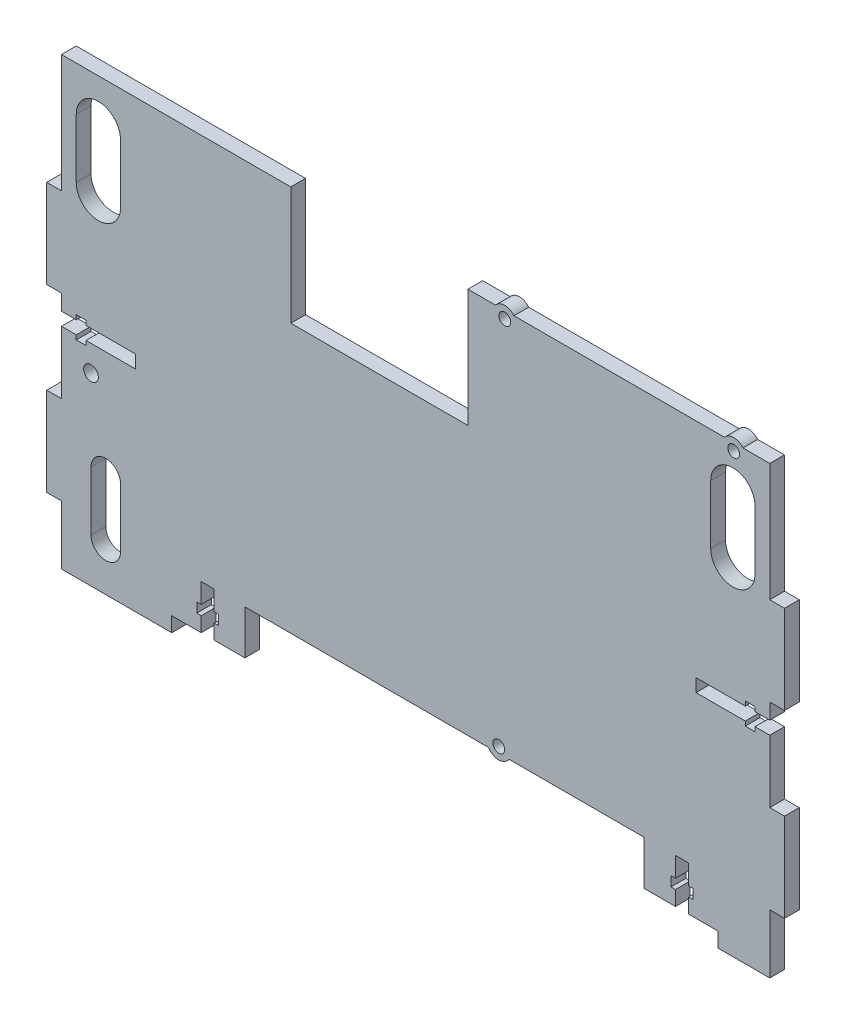
SolidWorks part; units mm, degrees
ref_plane "Front Plane" through (0, 0, 0) normal (0, 0, 1) x (1, 0, 0)
ref_plane "Top Plane" through (0, 0, 0) normal (0, 1, 0) x (1, 0, 0)
ref_plane "Right Plane" through (0, 0, 0) normal (1, 0, 0) x (0, 0, -1)
sketch "Sketch1" plane through (0, 0, 0) normal (0, 0, 1) x (1, 0, 0)
  line L1 (-120, 75.5) -> (120, 75.5)
  line L2 (-120, 75.5) -> (-120, -75.5)
  line L3 (-120, -75.5) -> (120, -75.5)
  line L4 (120, 75.5) -> (120, -75.5)
  dimension "D1" = 240
  dimension "D2" = 120
  dimension "D3" = 151
  dimension "D4" = 75.5
extrude "Boss-Extrude1" add sketch "Sketch1" along normal blind 5
sketch "Sketch2" plane through (0, 0, 0) normal (0, 0, -1) x (-1, 0, 0)
  line L1 (42.3015, 35.5) -> (42.3015, 75.5)
  line L3 (-17.6985, 75.5) -> (-17.6985, 35.5)
  line L4 (-120, 75.5) -> (120, 75.5) construction
  line L5 (42.3015, 35.5) -> (-17.6985, 35.5)
  line L6 (42.3015, 75.5) -> (-17.6985, 75.5)
  line L7 (-120, -75.5) -> (-120, 75.5) construction
  dimension "D1" = 60
  dimension "D2" = 102.3015
extrude "Cut-Extrude1" cut sketch "Sketch2" against normal blind 5
sketch "Sketch4" plane through (0, 0, 0) normal (0, 0, -1) x (-1, 0, 0)
  circle A0 centre (-107.8, 73) radius 2
  circle A1 centre (-30.2, 73) radius 2
  dimension "D1" = 4
  dimension "D2" = 4
extrude "Cut-Extrude3" cut sketch "Sketch4" against normal blind 5
sketch "Sketch5" plane through (0, 0, 0) normal (0, 0, -1) x (-1, 0, 0)
  circle A0 centre (-30.2, 73) radius 2
  circle A1 centre (-107.8, 73) radius 2
  circle A2 centre (-30.2, 73) radius 4
  circle A3 centre (-107.8, 73) radius 4
  dimension "D1" = 8
  dimension "D2" = 8
extrude "Boss-Extrude2" add sketch "Sketch5" against normal blind 5
sketch "Sketch6" plane through (0, 0, 0) normal (0, 0, -1) x (-1, 0, 0)
  circle A0 centre (117.5, 7.7) radius 2
  circle A1 centre (117.5, 63.3) radius 2
  dimension "D1" = 4
  dimension "D2" = 4
extrude "Cut-Extrude4" [suppressed] cut sketch "Sketch6" against normal blind 5
sketch "Sketch7" [suppressed] plane through (0, 0, 0) normal (0, 0, -1) x (-1, 0, 0)
  circle A0 centre (117.5, 7.7) radius 2
  circle A1 centre (117.5, 63.3) radius 1.9875
  circle A2 centre (117.5, 7.7) radius 4
  circle A3 centre (117.5, 63.3) radius 4
  dimension "D1" = 8
  dimension "D2" = 8
extrude "Boss-Extrude3" [suppressed] add sketch "Sketch7" against normal blind 5
sketch "Sketch8" plane through (0, 0, 0) normal (0, 0, -1) x (-1, 0, 0)
  line L0 (105, -60.5) -> (105, -40.5) construction
  line L1 (100, -60.5) -> (100, -40.5)
  line L2 (110, -60.5) -> (110, -40.5)
  line L3 (120, -75.5) -> (-120, -75.5) construction
  line L4 (120, 75.5) -> (120, -75.5) construction
  line L5 (0, 0) -> (0, -55.5387) construction
  arc A0 (100, -60.5) -> (110, -60.5) centre (105, -60.5) ccw
  arc A1 (110, -40.5) -> (100, -40.5) centre (105, -40.5) ccw
  point P2 (105, -50.5)
  point P17 (-92, -45.5)
  dimension "D1" = 20
  dimension "D2" = 15
  dimension "D3" = 10
  dimension "D4" = 10
extrude "Cut-Extrude5" cut sketch "Sketch8" against normal blind 5
sketch "Sketch9" plane through (0, 0, 0) normal (0, 0, -1) x (-1, 0, 0)
  circle A0 centre (117.5, 44.8) radius 2
  circle A1 centre (117.5, -10.8) radius 2
  dimension "D1" = 4
  dimension "D2" = 4
extrude "Cut-Extrude6" [suppressed] cut sketch "Sketch9" against normal blind 5
sketch "Sketch10" [suppressed] plane through (0, 0, 0) normal (0, 0, -1) x (-1, 0, 0)
  circle A0 centre (117.5, -10.8) radius 2
  circle A1 centre (117.5, -10.8) radius 4
  circle A2 centre (117.5, 44.8) radius 2
  circle A3 centre (117.5, 44.8) radius 4
  dimension "D1" = 8
  dimension "D2" = 8
extrude "Boss-Extrude4" [suppressed] add sketch "Sketch10" against normal blind 5
sketch "Sketch12" plane through (0, 0, 0) normal (0, 0, -1) x (-1, 0, 0)
  circle A0 centre (-28.1604, -53.4404) radius 2
  dimension "D1" = 4
extrude "Cut-Extrude7" cut sketch "Sketch12" against normal blind 5
sketch "Sketch13" plane through (0, 0, 0) normal (0, 0, -1) x (-1, 0, 0)
  circle A1 centre (110, -13) radius 2.5
extrude "Cut-Extrude8" cut sketch "Sketch13" against normal blind 10
sketch "Sketch14" plane through (0, 0, 0) normal (0, 0, -1) x (-1, 0, 0)
  line L0 (-104.6775, 75.5) -> (-33.3225, 75.5) construction
  line L1 (-120, -75.5) -> (-120, 75.5) construction
  line L2 (120, -75.5) -> (-120, -75.5) construction
  line L3 (120, 75.5) -> (120, -75.5) construction
  line L4 (42.3015, 75.5) -> (120, 75.5) construction
  circle A0 centre (-105, -60.5) radius 2.5
  circle A1 centre (105, -60.5) radius 2.5
  circle A2 centre (-105, 60.5) radius 2.5
  circle A3 centre (105, 60.5) radius 2.5
  dimension "D1" = 5
  dimension "D2" = 5
  dimension "D3" = 5
  dimension "D4" = 5
  dimension "D5" = 15
  dimension "D6" = 15
  dimension "D7" = 15
  dimension "D8" = 15
  dimension "D9" = 15
  dimension "D10" = 15
  dimension "D11" = 15
  dimension "D12" = 15
extrude "Cut-Extrude9" [suppressed] cut sketch "Sketch14" against normal blind 10
sketch "Sketch15" plane through (0, 0, 0) normal (0, 0, -1) x (-1, 0, 0)
  line L0 (-70, 0) -> (-50, 0) construction
  line L1 (-70, 7.5) -> (-50, 7.5)
  line L2 (-70, -7.5) -> (-50, -7.5)
  line L3 (50, 0) -> (70, 0) construction
  line L4 (50, 7.5) -> (70, 7.5)
  line L5 (50, -7.5) -> (70, -7.5)
  line L6 (-102.5, 55.5) -> (-102.5, 35.5) construction
  line L7 (-95, 55.5) -> (-95, 35.5)
  line L8 (-110, 55.5) -> (-110, 35.5)
  line L9 (-104.6775, 75.5) -> (-33.3225, 75.5) construction
  line L10 (-120, -75.5) -> (-120, 75.5) construction
  line L11 (0, 0) -> (0, 86.6929) construction
  line L12 (102.5, 55.5) -> (102.5, 35.5) construction
  line L13 (95, 55.5) -> (95, 35.5)
  line L14 (110, 55.5) -> (110, 35.5)
  arc A0 (-70, 7.5) -> (-70, -7.5) centre (-70, 0) ccw
  arc A1 (-50, -7.5) -> (-50, 7.5) centre (-50, 0) ccw
  arc A2 (50, 7.5) -> (50, -7.5) centre (50, 0) ccw
  arc A3 (70, -7.5) -> (70, 7.5) centre (70, 0) ccw
  arc A4 (-95, 55.5) -> (-110, 55.5) centre (-102.5, 55.5) ccw
  arc A5 (-110, 35.5) -> (-95, 35.5) centre (-102.5, 35.5) ccw
  arc A6 (95, 55.5) -> (110, 55.5) centre (102.5, 55.5) cw
  arc A7 (110, 35.5) -> (95, 35.5) centre (102.5, 35.5) cw
  point P2 (-60, 0)
  point P7 (60, 0)
  point P14 (-60, 7.5)
  point P15 (60, -7.5)
  point P16 (-102.5, 45.5)
  point P32 (102.5, 45.5)
  dimension "D1" = 20
  dimension "D2" = 20
  dimension "D3" = 50
  dimension "D4" = 50
  dimension "D5" = 15
  dimension "D6" = 15
  dimension "D7" = 15
  dimension "D8" = 20
  dimension "D9" = 20
  dimension "D10" = 10
extrude "Cut-Extrude10" [suppressed] cut sketch "Sketch15" against normal blind 10
sketch "Sketch16" plane through (0, 0, 0) normal (0, 0, -1) x (-1, 0, 0)
  line L0 (-120, -75.5) -> (-120, 75.5) construction
  line L9 (-120, 35.5) -> (-125, 35.5)
  line L10 (-120, 35.5) -> (-120, 5.5)
  line L11 (-120, 5.5) -> (-125, 5.5)
  line L12 (-125, 35.5) -> (-125, 5.5)
  line L13 (-120, -55.5) -> (-125, -55.5)
  line L14 (-120, -55.5) -> (-120, -25.5)
  line L15 (-120, -25.5) -> (-125, -25.5)
  line L16 (-125, -55.5) -> (-125, -25.5)
  line L18 (-120, 75.5) -> (-110.9225, 75.5) construction
  line L19 (120, -75.5) -> (-120, -75.5) construction
  line L20 (0, 0) -> (0, -42.8978) construction
  line L21 (125, -55.5) -> (125, -25.5)
  line L22 (120, -25.5) -> (125, -25.5)
  line L23 (120, -55.5) -> (120, -25.5)
  line L24 (120, -55.5) -> (125, -55.5)
  line L25 (125, 35.5) -> (125, 5.5)
  line L26 (120, 5.5) -> (125, 5.5)
  line L27 (120, 35.5) -> (120, 5.5)
  line L28 (120, 35.5) -> (125, 35.5)
  dimension "D1" = 40
  dimension "D2" = 30
  dimension "D3" = 5
  dimension "D4" = 20
  dimension "D5" = 30
  dimension "D6" = 5
extrude "Boss-Extrude5" add sketch "Sketch16" against normal blind 5
sketch "Sketch17" plane through (0, 0, 0) normal (0, 0, -1) x (-1, 0, 0)
  line L0 (0, 0) -> (0, 39.4066) construction
  line L1 (-120, 0.155) -> (-115, 0.155)
  line L2 (-115, 0.155) -> (-115, 1.655)
  line L3 (-115, 1.655) -> (-111.7, 1.655)
  line L4 (-111.7, 1.655) -> (-111.7, 0.155)
  line L5 (-111.7, 0.155) -> (-95, 0.155)
  line L6 (-95, 0.155) -> (-95, -4.245)
  line L7 (-95, -4.245) -> (-111.7, -4.245)
  line L8 (-111.7, -4.245) -> (-111.7, -5.745)
  line L9 (-111.7, -5.745) -> (-115, -5.745)
  line L10 (-115, -5.745) -> (-115, -4.245)
  line L11 (-115, -4.245) -> (-120, -4.245)
  line L12 (-120, -4.245) -> (-120, 0.155)
  line L15 (-120, 35.5) -> (-120, 75.5) construction
  line L16 (120, -4.245) -> (120, 0.155)
  line L17 (115, -4.245) -> (120, -4.245)
  line L18 (115, -5.745) -> (115, -4.245)
  line L19 (111.7, -5.745) -> (115, -5.745)
  line L20 (111.7, -4.245) -> (111.7, -5.745)
  line L21 (95, -4.245) -> (111.7, -4.245)
  line L22 (95, 0.155) -> (95, -4.245)
  line L23 (111.7, 0.155) -> (95, 0.155)
  line L24 (111.7, 1.655) -> (111.7, 0.155)
  line L25 (115, 1.655) -> (111.7, 1.655)
  line L26 (115, 0.155) -> (115, 1.655)
  line L27 (120, 0.155) -> (115, 0.155)
  dimension "D1" = 4.4
  dimension "D2" = 1.5
  dimension "D3" = 3.3
  dimension "D4" = 5
  dimension "D5" = 25
extrude "Cut-Extrude11" cut sketch "Sketch17" against normal blind 5
sketch "Sketch18" plane through (0, 0, 0) normal (0, 0, -1) x (-1, 0, 0)
  line L1 (-77.45, -55.5) -> (-77.45, -75.5)
  line L3 (57.85, -75.5) -> (57.85, -55.5)
  line L5 (-77.45, -55.5) -> (57.85, -55.5)
  line L7 (-77.45, -75.5) -> (57.85, -75.5)
  line L8 (120, -55.5) -> (120, -75.5) construction
  line L9 (-120, -75.5) -> (-120, -55.5) construction
  line L10 (120, -75.5) -> (-120, -75.5) construction
  point P8 (120, -65.5)
  dimension "D1" = 62.15
  dimension "D2" = 42.55
  dimension "D3" = 20
extrude "Cut-Extrude13" cut sketch "Sketch18" against normal blind 10
sketch "Sketch19" plane through (0, 0, 0) normal (0, 0, -1) x (-1, 0, 0)
  circle A0 centre (-28.1604, -53.4404) radius 2
  circle A1 centre (-28.1604, -53.4404) radius 4
  dimension "D1" = 8
extrude "Boss-Extrude6" add sketch "Sketch19" against normal blind 5
sketch "Sketch20" plane through (0, 0, 0) normal (0, 0, -1) x (-1, 0, 0)
  line L4 (57.85, -70.5) -> (57.85, -75.5)
  line L5 (57.85, -75.5) -> (82.65, -75.5)
  line L6 (82.65, -70.5) -> (82.65, -75.5)
  line L7 (57.85, -70.5) -> (82.65, -70.5)
  line L9 (57.85, -75.5) -> (57.85, -55.5) construction
  line L10 (120, -55.5) -> (120, -75.5) construction
  dimension "D1" = 37.35
extrude "Cut-Extrude14" cut sketch "Sketch20" against normal blind 5
sketch "Sketch21" plane through (0, 0, 0) normal (0, 0, -1) x (-1, 0, 0)
  line L0 (-120, -75.5) -> (-120, -55.5) construction
  line L1 (-77.45, -55.5) -> (-77.45, -75.5) construction
  line L8 (-102.45, -75.5) -> (-77.45, -75.5)
  line L9 (-102.45, -70.5) -> (-102.45, -75.5)
  line L10 (-77.45, -70.5) -> (-102.45, -70.5)
  line L11 (-77.45, -75.5) -> (-77.45, -70.5)
  dimension "D1" = 17.55
extrude "Cut-Extrude15" cut sketch "Sketch21" against normal blind 5
sketch "Sketch22" plane through (0, 0, 0) normal (0, 0, -1) x (-1, 0, 0)
  line L0 (68.25, -55.5) -> (68.25, -62.2)
  line L1 (82.65, -70.5) -> (57.85, -70.5) construction
  line L2 (68.25, -55.5) -> (72.65, -55.5)
  line L3 (72.65, -55.5) -> (72.65, -62.2)
  line L4 (72.65, -62.2) -> (74.15, -62.2)
  line L5 (74.15, -62.2) -> (74.15, -65.5)
  line L6 (74.15, -65.5) -> (72.65, -65.5)
  line L7 (72.65, -65.5) -> (72.65, -70.5)
  line L8 (68.25, -62.2) -> (66.75, -62.2)
  line L9 (66.75, -62.2) -> (66.75, -65.5)
  line L10 (66.75, -65.5) -> (68.25, -65.5)
  line L11 (68.25, -65.5) -> (68.25, -70.5)
  line L12 (68.25, -70.5) -> (72.65, -70.5)
  line L13 (70.45, -70.5) -> (70.45, -45.2903) construction
  line L14 (-92.45, -55.5) -> (-92.45, -62.2)
  line L15 (-92.45, -55.5) -> (-88.05, -55.5)
  line L16 (-88.05, -55.5) -> (-88.05, -62.2)
  line L17 (-88.05, -62.2) -> (-86.55, -62.2)
  line L18 (-86.55, -62.2) -> (-86.55, -65.5)
  line L19 (-86.55, -65.5) -> (-88.05, -65.5)
  line L20 (-88.05, -65.5) -> (-88.05, -70.5)
  line L21 (-92.45, -62.2) -> (-93.95, -62.2)
  line L22 (-93.95, -62.2) -> (-93.95, -65.5)
  line L23 (-93.95, -65.5) -> (-92.45, -65.5)
  line L24 (-92.45, -65.5) -> (-92.45, -70.5)
  line L25 (-92.45, -70.5) -> (-88.05, -70.5)
  line L26 (-90.25, -70.5) -> (-90.25, -50.7904) construction
  line L27 (-77.45, -70.5) -> (-102.45, -70.5) construction
  line L28 (82.65, -75.5) -> (82.65, -70.5) construction
  line L29 (-102.45, -70.5) -> (-102.45, -75.5) construction
  dimension "D1" = 4.4
  dimension "D2" = 1.5
  dimension "D3" = 3.3
  dimension "D4" = 5
  dimension "D5" = 15
  dimension "D6" = 4.4
  dimension "D7" = 1.5
  dimension "D8" = 3.3
  dimension "D9" = 15
  dimension "D10" = 5
  dimension "D11" = 10
  dimension "D12" = 10
extrude "Cut-Extrude16" cut sketch "Sketch22" against normal blind 5
sketch "Sketch23" plane through (0, 0, 0) normal (0, 0, -1) x (-1, 0, 0)
  line L0 (-107.5, 60.5) -> (-107.5, 40.5) construction
  line L1 (-100, 60.5) -> (-100, 40.5)
  line L2 (-115, 60.5) -> (-115, 40.5)
  line L3 (-120, 35.5) -> (-120, 75.5) construction
  line L4 (-104.6775, 75.5) -> (-33.3225, 75.5) construction
  line L5 (0, 0) -> (0, 68.359) construction
  line L6 (107.5, 60.5) -> (107.5, 40.5) construction
  line L7 (100, 60.5) -> (100, 40.5)
  line L8 (115, 60.5) -> (115, 40.5)
  arc A0 (-100, 60.5) -> (-115, 60.5) centre (-107.5, 60.5) ccw
  arc A1 (-115, 40.5) -> (-100, 40.5) centre (-107.5, 40.5) ccw
  arc A2 (100, 60.5) -> (115, 60.5) centre (107.5, 60.5) cw
  arc A3 (115, 40.5) -> (100, 40.5) centre (107.5, 40.5) cw
  point P0 (-107.5, 50.5)
  point P16 (107.5, 50.5)
  dimension "D1" = 15
  dimension "D2" = 20
  dimension "D3" = 5
  dimension "D4" = 15
extrude "Cut-Extrude17" cut sketch "Sketch23" against normal blind 10
